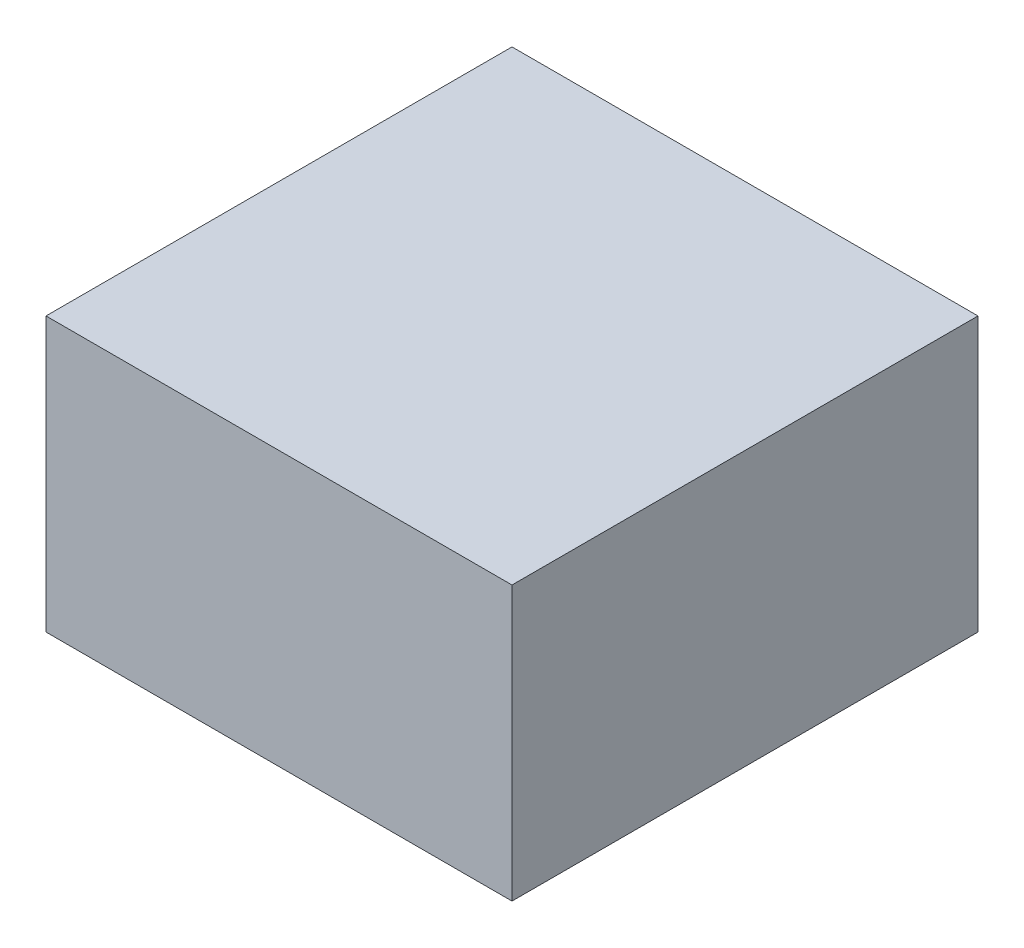
SolidWorks part; units mm, degrees
ref_plane "Front Plane" through (0, 0, 0) normal (0, 0, 1) x (1, 0, 0)
ref_plane "Top Plane" through (0, 0, 0) normal (0, 1, 0) x (1, 0, 0)
ref_plane "Right Plane" through (0, 0, 0) normal (1, 0, 0) x (0, 0, -1)
other "Center of Mass"
sketch "Sketch1" plane through (0, 0, 0) normal (0, 1, 0) x (1, 0, 0)
  line L1 (-24, 24) -> (24, 24)
  line L2 (-24, 24) -> (-24, -24)
  line L3 (-24, -24) -> (24, -24)
  line L4 (24, 24) -> (24, -24)
  dimension "D1" = 48
  dimension "D2" = 48
  dimension "D3" = 24
  dimension "D4" = 24
extrude "Boss-Extrude1" add sketch "Sketch1" along normal mid plane 28.2
